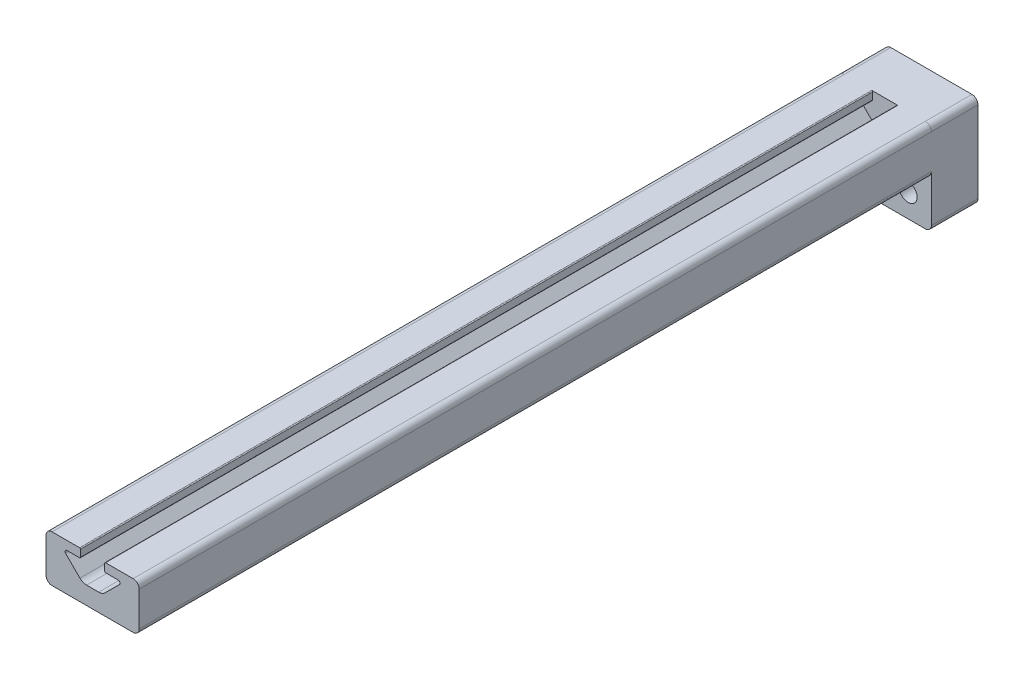
SolidWorks part; units mm, degrees
other "Imported1" parameters "D1"=215.9, "Length"=6096
ref_plane "Front" through (0, 0, 0) normal (0, 0, 1) x (1, 0, 0)
ref_plane "Top" through (0, 0, 0) normal (0, 1, 0) x (1, 0, 0)
ref_plane "Right" through (0, 0, 0) normal (1, 0, 0) x (0, 0, -1)
sketch "Sketch1" plane through (0, 0, 0) normal (0, 0, 1) x (1, 0, 0)
  line L0 (-3.302, 12.7) -> (3.302, 12.7) construction
  line L1 (-7.493, 9.8209) -> (7.493, 9.8209) construction
  line L2 (-11.049, 12.7) -> (-3.302, 12.7)
  line L3 (3.302, 12.7) -> (11.049, 12.7)
  line L4 (11.049, 0) -> (-11.049, 0)
  line L6 (-3.302, 12.7) -> (-3.302, 10.3289)
  line L7 (3.302, 12.7) -> (3.302, 10.3289)
  line L28 (-12.7, 11.049) -> (-12.7, 1.651)
  line L32 (12.7, 1.651) -> (12.7, 11.049)
  line L35 (3.302, 10.3289) -> (6.985, 10.3289)
  line L36 (7.3442, 9.4617) -> (3.4525, 5.5699)
  line L37 (1.6565, 4.826) -> (-1.6565, 4.826)
  line L38 (-3.4525, 5.5699) -> (-7.3442, 9.4617)
  line L39 (-6.985, 10.3289) -> (-3.302, 10.3289)
  arc A36 (-12.7, 1.651) -> (-11.049, 0) centre (-11.049, 1.651) ccw
  arc A41 (11.049, 0) -> (12.7, 1.651) centre (11.049, 1.651) ccw
  arc A42 (12.7, 11.049) -> (11.049, 12.7) centre (11.049, 11.049) ccw
  arc A46 (7.3442, 9.4617) -> (6.985, 10.3289) centre (6.985, 9.8209) ccw
  arc A47 (1.6565, 4.826) -> (3.4525, 5.5699) centre (1.6565, 7.366) ccw
  arc A48 (-3.4525, 5.5699) -> (-1.6565, 4.826) centre (-1.6565, 7.366) ccw
  arc A49 (-6.985, 10.3289) -> (-7.3442, 9.4617) centre (-6.985, 9.8209) ccw
  arc A53 (-11.049, 12.7) -> (-12.7, 11.049) centre (-11.049, 11.049) ccw
  point P8 (0, 0)
  point P10 (0, 4.826)
  point P11 (0, 9.8209)
  point P13 (0, 12.7)
  dimension "D6" = 1.651
  dimension "D7" = 0.508
  dimension "D12" = 2.54
  dimension "D1" = 6.604
  dimension "D2" = 14.986
  dimension "D4" = 25.4
  dimension "D5" = 12.7
  dimension "D10" = 7.874
  dimension "D11" = 2.3711
  dimension "D13" = 45
sketch "Sketch2" plane through (0, 0, 0) normal (1, 0, 0) x (0, 0, -1)
  line L0 (3048, 0) -> (-3048, 0) construction
  point P4 (0, 0)
sketch "Sketch3" plane through (0, 0, 0) normal (0, 0, 1) x (1, 0, 0)
  line L0 (-11.049, 12.7) -> (-3.302, 12.7) construction
  line L1 (-3.302, 12.7) -> (-3.302, 10.3289) construction
  line L2 (-6.985, 10.3289) -> (-3.302, 10.3289) construction
  line L3 (-3.4525, 5.5699) -> (-7.3442, 9.4617) construction
  line L4 (1.6565, 4.826) -> (-1.6565, 4.826) construction
  line L5 (7.3442, 9.4617) -> (3.4525, 5.5699) construction
  line L6 (3.302, 10.3289) -> (6.985, 10.3289) construction
  line L7 (3.302, 12.7) -> (3.302, 10.3289) construction
  line L8 (3.302, 12.7) -> (11.049, 12.7) construction
  line L9 (12.7, 1.651) -> (12.7, 11.049) construction
  line L10 (11.049, 0) -> (-11.049, 0) construction
  line L11 (-12.7, 11.049) -> (-12.7, 1.651) construction
  line L12 (-11.049, 12.7) -> (-3.302, 12.7)
  line L13 (-3.302, 12.7) -> (-3.302, 10.3289)
  line L14 (-6.985, 10.3289) -> (-3.302, 10.3289)
  line L15 (-3.4525, 5.5699) -> (-7.3442, 9.4617)
  line L16 (1.6565, 4.826) -> (-1.6565, 4.826)
  line L17 (7.3442, 9.4617) -> (3.4525, 5.5699)
  line L18 (3.302, 10.3289) -> (6.985, 10.3289)
  line L19 (3.302, 12.7) -> (3.302, 10.3289)
  line L20 (3.302, 12.7) -> (11.049, 12.7)
  line L21 (12.7, 1.651) -> (12.7, 11.049)
  line L22 (11.049, 0) -> (-11.049, 0)
  line L23 (-12.7, 11.049) -> (-12.7, 1.651)
  arc A2 (-6.985, 10.3289) -> (-7.3442, 9.4617) centre (-6.985, 9.8209) ccw construction
  arc A3 (-3.4525, 5.5699) -> (-1.6565, 4.826) centre (-1.6565, 7.366) ccw construction
  arc A4 (1.6565, 4.826) -> (3.4525, 5.5699) centre (1.6565, 7.366) ccw construction
  arc A5 (7.3442, 9.4617) -> (6.985, 10.3289) centre (6.985, 9.8209) ccw construction
  arc A6 (12.7, 11.049) -> (11.049, 12.7) centre (11.049, 11.049) ccw construction
  arc A7 (11.049, 0) -> (12.7, 1.651) centre (11.049, 1.651) ccw construction
  arc A8 (-12.7, 1.651) -> (-11.049, 0) centre (-11.049, 1.651) ccw construction
  arc A9 (-11.049, 12.7) -> (-12.7, 11.049) centre (-11.049, 11.049) ccw construction
  arc A12 (-6.985, 10.3289) -> (-7.3442, 9.4617) centre (-6.985, 9.8209) ccw
  arc A13 (-3.4525, 5.5699) -> (-1.6565, 4.826) centre (-1.6565, 7.366) ccw
  arc A14 (1.6565, 4.826) -> (3.4525, 5.5699) centre (1.6565, 7.366) ccw
  arc A15 (7.3442, 9.4617) -> (6.985, 10.3289) centre (6.985, 9.8209) ccw
  arc A16 (12.7, 11.049) -> (11.049, 12.7) centre (11.049, 11.049) ccw
  arc A17 (11.049, 0) -> (12.7, 1.651) centre (11.049, 1.651) ccw
  arc A18 (-12.7, 1.651) -> (-11.049, 0) centre (-11.049, 1.651) ccw
  arc A19 (-11.049, 12.7) -> (-12.7, 11.049) centre (-11.049, 11.049) ccw
extrude "Boss-Extrude1" add sketch "Sketch3" along normal blind 215.9
fillet "Fillet1" radius 0.254 4 edges at (3.302, 10.3289, 107.95) (3.302, 12.7, 107.95) (-3.302, 10.3289, 107.95) (-3.302, 12.7, 107.95)
sketch "Sketch4" plane through (0, 0, 0) normal (0, 0, -1) x (-1, 0, 0)
  line L0 (12.7, 11.049) -> (12.7, 1.651) construction
  line L1 (-12.7, -12.7) -> (12.7, -12.7)
  line L2 (-12.7, -12.7) -> (-12.7, 12.7)
  line L3 (-12.7, 12.7) -> (12.7, 12.7)
  line L4 (12.7, -12.7) -> (12.7, 12.7)
  line L5 (-12.7, 1.651) -> (-12.7, 11.049) construction
  line L6 (3.556, 12.7) -> (11.049, 12.7) construction
  dimension "D1" = 25.4
extrude "Boss-Extrude2" add sketch "Sketch4" along normal blind 12.7
fillet "Fillet2" radius 1.651 4 edges at (-12.7, 12.7, -6.35) (12.7, 12.7, -6.35) (-12.7, -12.7, -6.35) (12.7, -12.7, -6.35)
hole_wizard "#10 (0.1935) Diameter Hole1" positions "Sketch5" profile "Sketch6" hole size "#10" standard "ANSI Inch"
sketch "Sketch5" plane through (0, 0, -12.7) normal (0, 0, -1) x (-1, 0, 0)
  line L0 (0, 0) -> (0, -19.0434) construction
  point P0 (-6.35, -6.35)
  point P8 (6.35, -6.35)
  dimension "D1" = 6.35
  dimension "D2" = 6.35
sketch "Sketch6" plane through (6.35, -6.35, -12.7) normal (1, 0, 0) x (0, 1, 0)
  line L0 (0, 0) -> (0, 25.4)
  line L1 (0, 25.4) -> (2.4574, 23.9234)
  line L2 (2.4574, 23.9234) -> (2.4574, 0)
  line L5 (2.4574, 0) -> (0, 0)
  line L10 (0, 25.4) -> (-2.4575, 23.9234) construction
  line L11 (0, -6.35) -> (0, 107.95) construction
  dimension "Hole Dia." = 4.9149
  dimension "Hole Depth" = 25.4
  dimension "Drill Angle" = 118
equation "\"D1@Boss-Extrude1\"=\"Length@Sketch2\""
